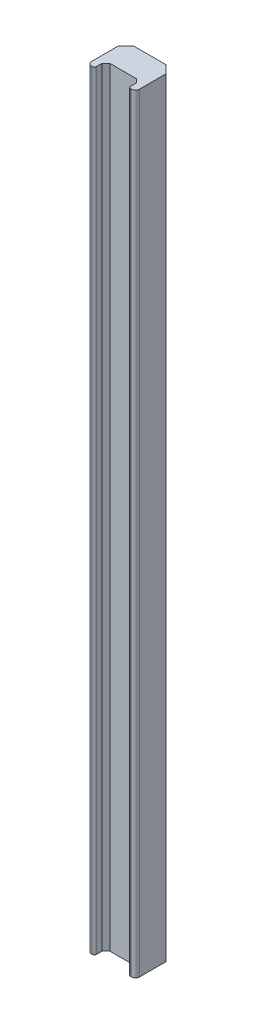
SolidWorks part; units mm, degrees
ref_plane "Front Plane" through (0, 0, 0) normal (0, 0, 1) x (1, 0, 0)
ref_plane "Top Plane" through (0, 0, 0) normal (0, 1, 0) x (1, 0, 0)
ref_plane "Right Plane" through (0, 0, 0) normal (1, 0, 0) x (0, 0, -1)
sketch "Sketch1" plane through (0, 0, 0) normal (0, 1, 0) x (1, 0, 0)
  line L0 (0, 8) -> (2, 10)
  line L1 (1, 0) -> (11.48, 0)
  line L2 (0, 1) -> (0, 8)
  line L3 (2, 10) -> (10.48, 10)
  line L4 (12.48, 1) -> (12.48, 8)
  line L5 (10.48, 10) -> (12.48, 8)
  arc A0 (11.48, 0) -> (12.48, 1) centre (11.48, 1) ccw
  arc A1 (1, 0) -> (0, 1) centre (1, 1) cw
  point P1 (12.48, 10)
  point P2 (0, 10)
  point P9 (0, 0)
  dimension "D1" = 1
  dimension "D2" = 12.48
  dimension "D3" = 9
extrude "Boss-Extrude1" add sketch "Sketch1" along normal blind 200
sketch "Sketch2" plane through (0, 0, -10) normal (0, 0, -1) x (-1, 0, 0)
  line L1 (-12.48, 175) -> (0, 175)
  line L2 (-12.48, 175) -> (-12.48, 169)
  line L3 (-12.48, 169) -> (0, 169)
  line L4 (0, 175) -> (0, 169)
  line L11 (-10.48, 200) -> (-2, 200) construction
  line L12 (-12.48, 200) -> (-12.48, 0) construction
  line L13 (0, 200) -> (0, 0) construction
  line L14 (-10.48, 100) -> (-2, 100) construction
  line L15 (-10.48, 200) -> (-10.48, 0) construction
  line L16 (-2, 200) -> (-2, 0) construction
  line L17 (-12.48, 31) -> (0, 31)
  line L18 (0, 25) -> (0, 31)
  line L19 (-12.48, 25) -> (0, 25)
  line L20 (-12.48, 25) -> (-12.48, 31)
  dimension "D2" = 25
  dimension "D3" = 6
extrude "Cut-Extrude1" cut sketch "Sketch2" against normal blind 2
sketch "Sketch3" plane through (0, 0, 0) normal (0, -1, 0) x (1, 0, 0)
  line L0 (1.79, 0) -> (1.79, -2)
  line L1 (1.79, -2) -> (2.79, -3)
  line L2 (6.24, 0) -> (6.24, -10) construction
  line L3 (10.48, -10) -> (2, -10) construction
  line L4 (10.69, -2) -> (10.69, 0)
  line L5 (1, 0) -> (11.48, 0) construction
  line L6 (1.79, 0) -> (10.69, 0) construction
  line L7 (1.79, 0) -> (10.69, 0)
  line L8 (10.69, -2) -> (9.69, -3)
  line L9 (9.69, -3) -> (2.79, -3)
  point P11 (6.24, 0)
  dimension "D1" = 8.9
  dimension "D2" = 1
  dimension "D3" = 1
  dimension "D4" = 3
extrude "Cut-Extrude2" cut sketch "Sketch3" against normal through all
fillet "Fillet1" radius 0.5 2 edges at (10.69, 100, 0) (1.79, 100, 0)
